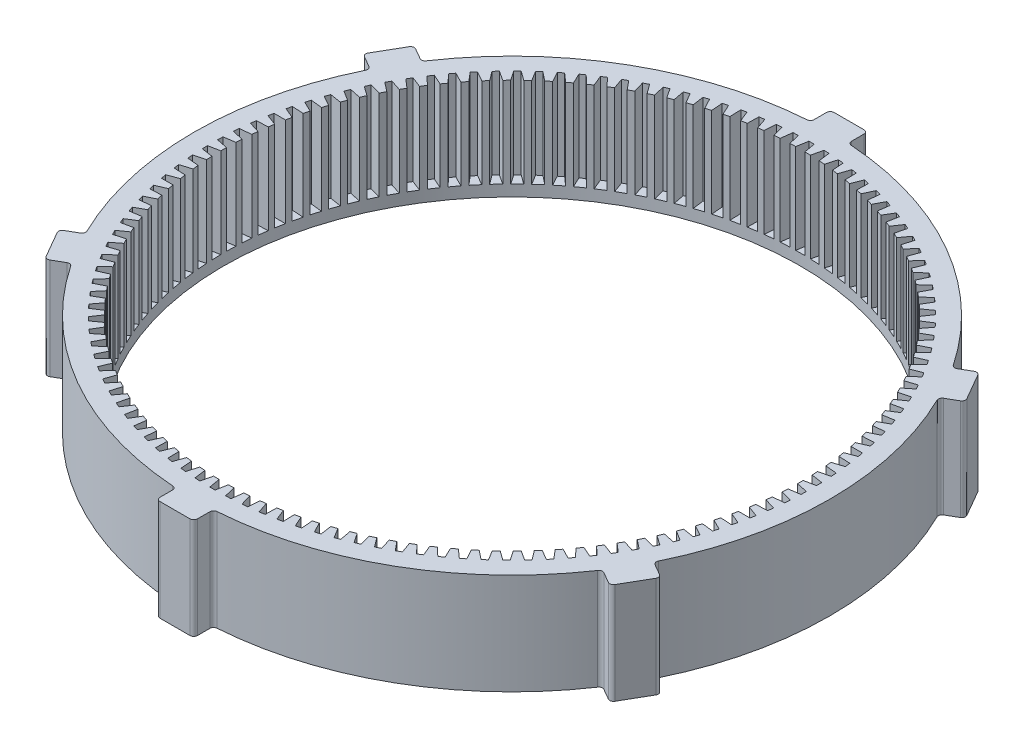
SolidWorks part; units mm, degrees
ref_plane "Front Plane" through (0, 0, 0) normal (0, 0, 1) x (1, 0, 0)
ref_plane "Top Plane" through (0, 0, 0) normal (0, 1, 0) x (1, 0, 0)
ref_plane "Right Plane" through (0, 0, 0) normal (1, 0, 0) x (0, 0, -1)
sketch "Sketch1" plane through (0, 0, 0) normal (0, 1, 0) x (1, 0, 0)
  circle A0 centre (0, 0) radius 38.5
  circle A1 centre (0, 0) radius 42.45
  point P5 (-1.9854, 0)
  dimension "D1" = 84.9
  dimension "D2" = 77
extrude "Boss-Extrude1" add sketch "Sketch1" along normal blind 13.5
sketch "Sketch2" plane through (0, 0, 0) normal (0, 1, 0) x (1, 0, 0)
  line L1 (2.5, -45) -> (-2.5, -45)
  line L2 (2.5, -45) -> (2.5, 45)
  line L3 (2.5, 45) -> (-2.5, 45)
  line L4 (-2.5, -45) -> (-2.5, 45)
  line L5 (0, 45) -> (0, -45) construction
  line L6 (2.5, 0) -> (-2.5, 0) construction
  circle A0 centre (0, 0) radius 42.45 construction
  circle A1 centre (0, 0) radius 42.45
  dimension "D1" = 5
  dimension "D2" = 90
extrude "Boss-Extrude2" add sketch "Sketch2" along normal up to surface (13.5 mm away) contours A1 L2 L3 L4 | A1 L4 L1 L2 up to face at (0, 13.5, 42.45)
pattern_circular "CirPattern1" count 3 over 360 about axis through (0, 0, 0) along (0, 1, 0) of "Boss-Extrude2"
fillet "Fillet1" radius 0.5 24 edges at (-2.5, 6.75, -42.3763) (-2.5, 6.75, 42.3763) (-2.5, 6.75, -45) (2.5, 6.75, -45) (2.5, 6.75, -42.3763) (2.5, 6.75, 42.3763) (-37.949, 6.75, 19.0231) (35.449, 6.75, -23.3532) (37.7211, 6.75, -24.6651) (40.2211, 6.75, -20.3349) (-35.449, 6.75, 23.3532) (37.949, 6.75, -19.0231) (37.949, 6.75, 19.0231) (-35.449, 6.75, -23.3532) (40.2211, 6.75, 20.3349) (37.7211, 6.75, 24.6651) (35.449, 6.75, 23.3532) (-37.949, 6.75, -19.0231) (2.5, 6.75, 45) (-2.5, 6.75, 45) (-37.7211, 6.75, 24.6651) (-40.2211, 6.75, 20.3349) (-40.2211, 6.75, -20.3349) (-37.7211, 6.75, -24.6651)
sketch "Sketch3" plane through (0, 13.5, 0) normal (0, 1, 0) x (1, 0, 0)
  line L0 (0, 38.5) -> (0, 40) construction
  line L1 (-0.35, 40) -> (0.35, 40)
  line L2 (-0.35, 40) -> (-0.6154, 38.4951)
  line L3 (-0.6154, 38.4951) -> (0.6154, 38.4951)
  line L4 (0.6154, 38.4951) -> (0.35, 40)
  circle A0 centre (0, 0) radius 38.5 construction
  point P8 (0, 0)
  dimension "D1" = 0.7
  dimension "D2" = 1.5
  dimension "D3" = 20
extrude "Cut-Extrude1" cut sketch "Sketch3" against normal blind 12
pattern_circular "CirPattern2" count 122 over 360 about axis through (0, 0, 0) along (0, 1, 0) of "Cut-Extrude1"
